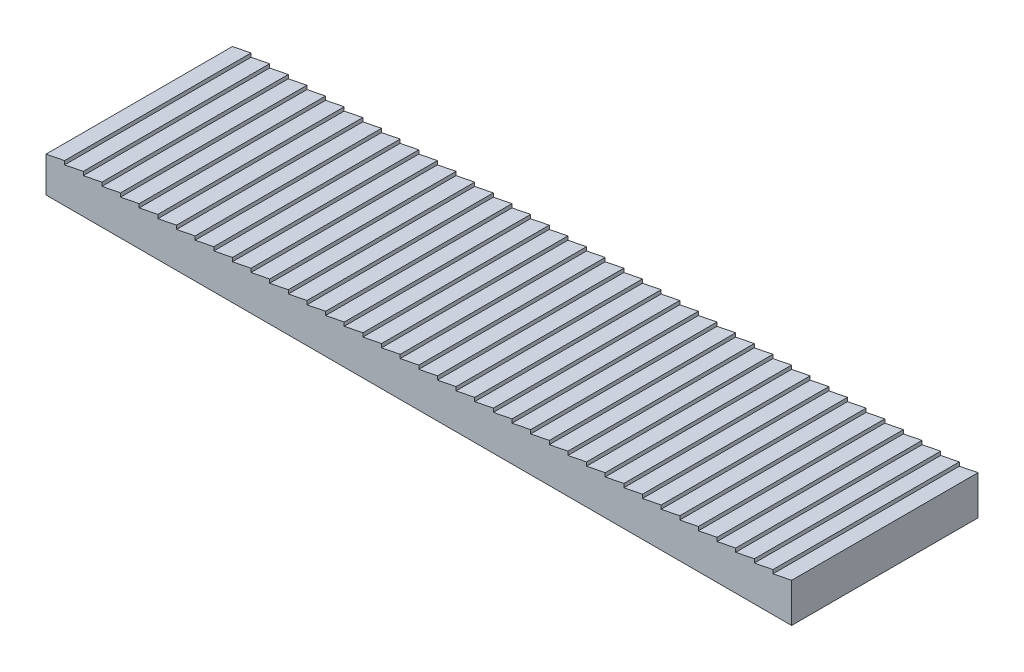
SolidWorks part; units mm, degrees
ref_plane "Ebene vorne" through (0, 0, 0) normal (0, 0, 1) x (1, 0, 0)
ref_plane "Ebene oben" through (0, 0, 0) normal (0, 1, 0) x (1, 0, 0)
ref_plane "Ebene rechts" through (0, 0, 0) normal (1, 0, 0) x (0, 0, -1)
sketch "Skizze1" plane through (0, 0, 0) normal (0, 0, 1) x (1, 0, 0)
  line L2 (200, -9.5) -> (0, -9.5)
  line L3 (0, -9.5) -> (0, 0)
  line L4 (0, 0) -> (200, 0) construction
  line L5 (200, 6.6947) -> (200, 0)
  line L6 (200, 0) -> (200, -9.5)
  line L7 (0, 0) -> (5, 1)
  line L8 (5, 1) -> (5, 0)
  line L9 (0, 0) -> (0, 0.5) construction
  line L10 (0, 0.5) -> (200, 0.5) construction
  line L11 (5, 0) -> (10, 1)
  line L12 (10, 1) -> (10, 0)
  line L13 (10, 0) -> (15, 1)
  line L14 (15, 1) -> (15, 0)
  line L15 (15, 0) -> (20, 1)
  line L16 (20, 1) -> (20, 0)
  line L17 (20, 0) -> (25, 1)
  line L18 (25, 1) -> (25, 0)
  line L19 (25, 0) -> (30, 1)
  line L20 (30, 1) -> (30, 0)
  line L21 (30, 0) -> (35, 1)
  line L22 (35, 1) -> (35, 0)
  line L23 (35, 0) -> (40, 1)
  line L24 (40, 1) -> (40, 0)
  line L25 (40, 0) -> (45, 1)
  line L26 (45, 1) -> (45, 0)
  line L27 (45, 0) -> (50, 1)
  line L28 (50, 1) -> (50, 0)
  line L29 (50, 0) -> (55, 1)
  line L30 (55, 1) -> (55, 0)
  line L31 (55, 0) -> (60, 1)
  line L32 (60, 1) -> (60, 0)
  line L33 (60, 0) -> (65, 1)
  line L34 (65, 1) -> (65, 0)
  line L35 (65, 0) -> (70, 1)
  line L36 (70, 1) -> (70, 0)
  line L37 (70, 0) -> (75, 1)
  line L38 (75, 1) -> (75, 0)
  line L39 (75, 0) -> (80, 1)
  line L40 (80, 1) -> (80, 0)
  line L41 (80, 0) -> (85, 1)
  line L42 (85, 1) -> (85, 0)
  line L43 (85, 0) -> (90, 1)
  line L44 (90, 1) -> (90, 0)
  line L45 (90, 0) -> (95, 1)
  line L46 (95, 1) -> (95, 0)
  line L47 (95, 0) -> (100, 1)
  line L48 (100, 1) -> (100, 0)
  line L49 (100, 0) -> (105, 1)
  line L50 (105, 1) -> (105, 0)
  line L51 (105, 0) -> (110, 1)
  line L52 (110, 1) -> (110, 0)
  line L53 (110, 0) -> (115, 1)
  line L54 (115, 1) -> (115, 0)
  line L55 (115, 0) -> (120, 1)
  line L56 (120, 1) -> (120, 0)
  line L57 (120, 0) -> (125, 1)
  line L58 (125, 1) -> (125, 0)
  line L59 (125, 0) -> (130, 1)
  line L60 (130, 1) -> (130, 0)
  line L61 (130, 0) -> (135, 1)
  line L62 (135, 1) -> (135, 0)
  line L63 (135, 0) -> (140, 1)
  line L64 (140, 1) -> (140, 0)
  line L65 (140, 0) -> (145, 1)
  line L66 (145, 1) -> (145, 0)
  line L67 (145, 0) -> (150, 1)
  line L68 (150, 1) -> (150, 0)
  line L69 (150, 0) -> (155, 1)
  line L70 (155, 1) -> (155, 0)
  line L71 (155, 0) -> (160, 1)
  line L72 (160, 1) -> (160, 0)
  line L73 (160, 0) -> (165, 1)
  line L74 (165, 1) -> (165, 0)
  line L75 (165, 0) -> (170, 1)
  line L76 (170, 1) -> (170, 0)
  line L77 (170, 0) -> (175, 1)
  line L78 (175, 1) -> (175, 0)
  line L79 (175, 0) -> (180, 1)
  line L80 (180, 1) -> (180, 0)
  line L81 (180, 0) -> (185, 1)
  line L82 (185, 1) -> (185, 0)
  line L83 (185, 0) -> (190, 1)
  line L84 (190, 1) -> (190, 0)
  line L85 (190, 0) -> (195, 1)
  line L86 (195, 1) -> (195, 0)
  line L87 (195, 0) -> (200, 1)
  line L88 (200, 1) -> (200, 0)
  line L89 (0, 0) -> (5, 0) construction
  line L90 (5, 0) -> (5, -9.5)
  point P11 (5, 0.5)
  dimension "D1" = 10
  dimension "D2" = 200
  dimension "D3" = 0.5
  dimension "D4" = 5
  dimension "D6" = 5
  dimension "D5" = 40
extrude "Aufsatz-Linear austragen1" add sketch "Skizze1" along normal blind 50 contours L90 L8 L7 L3 L2 | L11 L90 L2 L6 L5 L87 L86 L85 L84 L83 L82 L81 L80 L79 L78 L77 L76 L75 L74 L73 L72 L71 L70 L69 L68 L67 L66 L65 L64 L63 L62 L61 L60 L59 L58 L57 L56 L55 L54 L53 L52 L51 L50 L49 L48 L47 L46 L45 L44 L43 L42
